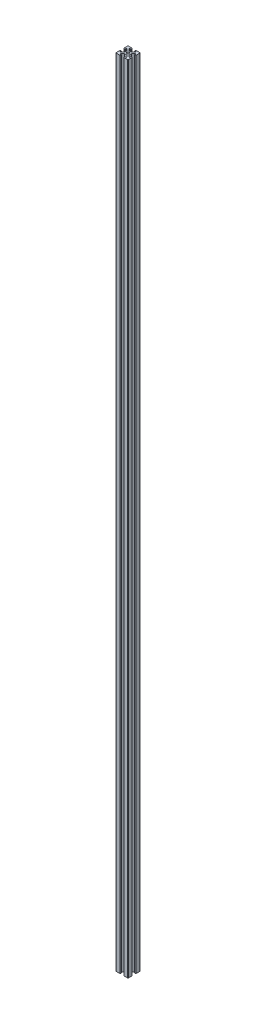
SolidWorks part; units mm, degrees
ref_plane "정면" through (0, 0, 0) normal (0, 0, 1) x (1, 0, 0)
ref_plane "윗면" through (0, 0, 0) normal (0, 1, 0) x (1, 0, 0)
ref_plane "우측면" through (0, 0, 0) normal (1, 0, 0) x (0, 0, -1)
sketch "스케치1" plane through (0, 0, 0) normal (0, 1, 0) x (1, 0, 0)
  line L0 (0, 4) -> (0, -4) construction
  line L1 (2, -4) -> (-2, -4)
  line L2 (-2, -4) -> (-5, -7)
  line L3 (-5, -7) -> (-5, -8) construction
  line L4 (-5, -8) -> (-2.6, -8) construction
  line L5 (-2.6, -8) -> (-2.6, -9.5) construction
  line L6 (-2.6, -9.5) -> (-3.1, -9.5)
  line L7 (-3.1, -9.5) -> (-3.1, -10)
  line L8 (-3.1, -10) -> (-9, -10)
  line L9 (-9, -10) -> (-9, -9) construction
  line L10 (-9, -10) -> (-10, -10) construction
  line L11 (-9, -9) -> (-10, -9) construction
  line L12 (-10, -10) -> (-10, -9) construction
  line L13 (3.1, -8) -> (3.1, -8.5) construction
  line L14 (2.6, -8.5) -> (3.1, -8.5) construction
  line L15 (2.6, -8) -> (2.6, -8.5) construction
  line L16 (-5, -7) -> (-5, -7.5)
  line L17 (-5, -8) -> (-4.5, -8) construction
  line L18 (-5, -8) -> (-5, -7.5) construction
  line L19 (-5, -7.5) -> (-4.5, -7.5) construction
  line L20 (-4.5, -8) -> (-4.5, -7.5) construction
  line L21 (-2.6, -9.5) -> (-2.6, -8.5)
  line L22 (-2.6, -8) -> (-3.1, -8) construction
  line L23 (-2.6, -8) -> (-2.6, -8.5) construction
  line L24 (-2.6, -8.5) -> (-3.1, -8.5) construction
  line L25 (-3.1, -8) -> (-3.1, -8.5) construction
  line L26 (-4.5, -8) -> (-3.1, -8)
  line L27 (2.6, -8) -> (3.1, -8) construction
  line L28 (4.5, -8) -> (4.5, -7.5) construction
  line L29 (5, -7.5) -> (4.5, -7.5) construction
  line L30 (5, -8) -> (5, -7.5) construction
  line L31 (5, -8) -> (4.5, -8) construction
  line L32 (10, -10) -> (10, -9) construction
  line L33 (9, -9) -> (10, -9) construction
  line L34 (9, -10) -> (10, -10) construction
  line L35 (9, -10) -> (9, -9) construction
  line L36 (2.6, -8) -> (2.6, -9.5) construction
  line L37 (5, -8) -> (2.6, -8) construction
  line L38 (5, -7) -> (5, -8) construction
  line L39 (4.5, -8) -> (3.1, -8)
  line L40 (2.6, -9.5) -> (2.6, -8.5)
  line L41 (5, -7) -> (5, -7.5)
  line L42 (3.1, -10) -> (9, -10)
  line L43 (3.1, -9.5) -> (3.1, -10)
  line L44 (2.6, -9.5) -> (3.1, -9.5)
  line L45 (2, -4) -> (5, -7)
  line L46 (-4, -2) -> (-4, 2)
  line L47 (-4, 2) -> (-7, 5)
  line L48 (-9.5, 2.6) -> (-9.5, 3.1)
  line L49 (-9.5, 3.1) -> (-10, 3.1)
  line L50 (-10, 3.1) -> (-10, 9)
  line L51 (-7, 5) -> (-7.5, 5)
  line L52 (-9.5, 2.6) -> (-8.5, 2.6)
  line L53 (-8, 4.5) -> (-8, 3.1)
  line L54 (-8, -4.5) -> (-8, -3.1)
  line L55 (-9.5, -2.6) -> (-8.5, -2.6)
  line L56 (-7, -5) -> (-7.5, -5)
  line L57 (-10, -3.1) -> (-10, -9)
  line L58 (-9.5, -3.1) -> (-10, -3.1)
  line L59 (-9.5, -2.6) -> (-9.5, -3.1)
  line L60 (-4, -2) -> (-7, -5)
  line L61 (4, 0) -> (-4, 0) construction
  line L62 (-7, 5) -> (-8, 5) construction
  line L63 (-8, 5) -> (-8, 2.6) construction
  line L64 (-8, 2.6) -> (-9.5, 2.6) construction
  line L65 (-10, 9) -> (-9, 9) construction
  line L66 (-10, 9) -> (-10, 10) construction
  line L67 (-9, 9) -> (-9, 10) construction
  line L68 (-10, 10) -> (-9, 10) construction
  line L69 (-8, -3.1) -> (-8.5, -3.1) construction
  line L70 (-8.5, -2.6) -> (-8.5, -3.1) construction
  line L71 (-8, -2.6) -> (-8.5, -2.6) construction
  line L72 (-8, 5) -> (-8, 4.5) construction
  line L73 (-8, 5) -> (-7.5, 5) construction
  line L74 (-7.5, 5) -> (-7.5, 4.5) construction
  line L75 (-8, 4.5) -> (-7.5, 4.5) construction
  line L76 (-8, 2.6) -> (-8, 3.1) construction
  line L77 (-8, 2.6) -> (-8.5, 2.6) construction
  line L78 (-8.5, 2.6) -> (-8.5, 3.1) construction
  line L79 (-8, 3.1) -> (-8.5, 3.1) construction
  line L80 (-8, -2.6) -> (-8, -3.1) construction
  line L81 (-8, -4.5) -> (-7.5, -4.5) construction
  line L82 (-7.5, -5) -> (-7.5, -4.5) construction
  line L83 (-8, -5) -> (-7.5, -5) construction
  line L84 (-8, -5) -> (-8, -4.5) construction
  line L85 (-10, -10) -> (-9, -10) construction
  line L86 (-9, -9) -> (-9, -10) construction
  line L87 (-10, -9) -> (-10, -10) construction
  line L88 (-10, -9) -> (-9, -9) construction
  line L89 (-8, -2.6) -> (-9.5, -2.6) construction
  line L90 (-8, -5) -> (-8, -2.6) construction
  line L91 (-7, -5) -> (-8, -5) construction
  line L92 (-2, 4) -> (2, 4)
  line L93 (2, 4) -> (5, 7)
  line L94 (2.6, 9.5) -> (3.1, 9.5)
  line L95 (3.1, 9.5) -> (3.1, 10)
  line L96 (3.1, 10) -> (9, 10)
  line L97 (5, 7) -> (5, 7.5)
  line L98 (2.6, 9.5) -> (2.6, 8.5)
  line L99 (4.5, 8) -> (3.1, 8)
  line L100 (-4.5, 8) -> (-3.1, 8)
  line L101 (-2.6, 9.5) -> (-2.6, 8.5)
  line L102 (-5, 7) -> (-5, 7.5)
  line L103 (-3.1, 10) -> (-9, 10)
  line L104 (-3.1, 9.5) -> (-3.1, 10)
  line L105 (-2.6, 9.5) -> (-3.1, 9.5)
  line L106 (-2, 4) -> (-5, 7)
  line L107 (0, -4) -> (0, 4) construction
  line L108 (5, 7) -> (5, 8) construction
  line L109 (5, 8) -> (2.6, 8) construction
  line L110 (2.6, 8) -> (2.6, 9.5) construction
  line L111 (9, 10) -> (9, 9) construction
  line L112 (9, 10) -> (10, 10) construction
  line L113 (9, 9) -> (10, 9) construction
  line L114 (10, 10) -> (10, 9) construction
  line L115 (-3.1, 8) -> (-3.1, 8.5) construction
  line L116 (-2.6, 8.5) -> (-3.1, 8.5) construction
  line L117 (-2.6, 8) -> (-2.6, 8.5) construction
  line L118 (5, 8) -> (4.5, 8) construction
  line L119 (5, 8) -> (5, 7.5) construction
  line L120 (5, 7.5) -> (4.5, 7.5) construction
  line L121 (4.5, 8) -> (4.5, 7.5) construction
  line L122 (2.6, 8) -> (3.1, 8) construction
  line L123 (2.6, 8) -> (2.6, 8.5) construction
  line L124 (2.6, 8.5) -> (3.1, 8.5) construction
  line L125 (3.1, 8) -> (3.1, 8.5) construction
  line L126 (-2.6, 8) -> (-3.1, 8) construction
  line L127 (-4.5, 8) -> (-4.5, 7.5) construction
  line L128 (-5, 7.5) -> (-4.5, 7.5) construction
  line L129 (-5, 8) -> (-5, 7.5) construction
  line L130 (-5, 8) -> (-4.5, 8) construction
  line L131 (-10, 10) -> (-10, 9) construction
  line L132 (-9, 9) -> (-10, 9) construction
  line L133 (-9, 10) -> (-10, 10) construction
  line L134 (-9, 10) -> (-9, 9) construction
  line L135 (-2.6, 8) -> (-2.6, 9.5) construction
  line L136 (-5, 8) -> (-2.6, 8) construction
  line L137 (-5, 7) -> (-5, 8) construction
  line L138 (4, 2) -> (4, -2)
  line L139 (4, -2) -> (7, -5)
  line L140 (9.5, -2.6) -> (9.5, -3.1)
  line L141 (9.5, -3.1) -> (10, -3.1)
  line L142 (10, -3.1) -> (10, -9)
  line L143 (7, -5) -> (7.5, -5)
  line L144 (9.5, -2.6) -> (8.5, -2.6)
  line L145 (8, -4.5) -> (8, -3.1)
  line L146 (8, 4.5) -> (8, 3.1)
  line L147 (9.5, 2.6) -> (8.5, 2.6)
  line L148 (7, 5) -> (7.5, 5)
  line L149 (10, 3.1) -> (10, 9)
  line L150 (9.5, 3.1) -> (10, 3.1)
  line L151 (9.5, 2.6) -> (9.5, 3.1)
  line L152 (4, 2) -> (7, 5)
  line L153 (-4, 0) -> (4, 0) construction
  line L154 (7, -5) -> (8, -5) construction
  line L155 (8, -5) -> (8, -2.6) construction
  line L156 (8, -2.6) -> (9.5, -2.6) construction
  line L157 (10, -9) -> (9, -9) construction
  line L158 (10, -9) -> (10, -10) construction
  line L159 (9, -9) -> (9, -10) construction
  line L160 (10, -10) -> (9, -10) construction
  line L161 (8, 3.1) -> (8.5, 3.1) construction
  line L162 (8.5, 2.6) -> (8.5, 3.1) construction
  line L163 (8, 2.6) -> (8.5, 2.6) construction
  line L164 (8, -5) -> (8, -4.5) construction
  line L165 (8, -5) -> (7.5, -5) construction
  line L166 (7.5, -5) -> (7.5, -4.5) construction
  line L167 (8, -4.5) -> (7.5, -4.5) construction
  line L168 (8, -2.6) -> (8, -3.1) construction
  line L169 (8, -2.6) -> (8.5, -2.6) construction
  line L170 (8.5, -2.6) -> (8.5, -3.1) construction
  line L171 (8, -3.1) -> (8.5, -3.1) construction
  line L172 (8, 2.6) -> (8, 3.1) construction
  line L173 (8, 4.5) -> (7.5, 4.5) construction
  line L174 (7.5, 5) -> (7.5, 4.5) construction
  line L175 (8, 5) -> (7.5, 5) construction
  line L176 (8, 5) -> (8, 4.5) construction
  line L177 (10, 10) -> (9, 10) construction
  line L178 (9, 9) -> (9, 10) construction
  line L179 (10, 9) -> (10, 10) construction
  line L180 (10, 9) -> (9, 9) construction
  line L181 (8, 2.6) -> (9.5, 2.6) construction
  line L182 (8, 5) -> (8, 2.6) construction
  line L183 (7, 5) -> (8, 5) construction
  circle A0 centre (0, 0) radius 2.1
  arc A1 (-5, -7.5) -> (-4.5, -8) centre (-4.5, -7.5) ccw
  arc A2 (-3.1, -8) -> (-2.6, -8.5) centre (-3.1, -8.5) cw
  arc A3 (-9, -10) -> (-9.7071, -9.7071) centre (-9, -9) cw
  arc A4 (9, -10) -> (9.7071, -9.7071) centre (9, -9) ccw
  arc A5 (3.1, -8) -> (2.6, -8.5) centre (3.1, -8.5) ccw
  arc A6 (5, -7.5) -> (4.5, -8) centre (4.5, -7.5) cw
  arc A7 (-7.5, 5) -> (-8, 4.5) centre (-7.5, 4.5) ccw
  arc A8 (-8, 3.1) -> (-8.5, 2.6) centre (-8.5, 3.1) cw
  arc A9 (-10, 9) -> (-9.7071, 9.7071) centre (-9, 9) cw
  arc A10 (-10, -9) -> (-9.7071, -9.7071) centre (-9, -9) ccw
  arc A11 (-8, -3.1) -> (-8.5, -2.6) centre (-8.5, -3.1) ccw
  arc A12 (-7.5, -5) -> (-8, -4.5) centre (-7.5, -4.5) cw
  arc A13 (5, 7.5) -> (4.5, 8) centre (4.5, 7.5) ccw
  arc A14 (3.1, 8) -> (2.6, 8.5) centre (3.1, 8.5) cw
  arc A15 (9, 10) -> (9.7071, 9.7071) centre (9, 9) cw
  arc A16 (-9, 10) -> (-9.7071, 9.7071) centre (-9, 9) ccw
  arc A17 (-3.1, 8) -> (-2.6, 8.5) centre (-3.1, 8.5) ccw
  arc A18 (-5, 7.5) -> (-4.5, 8) centre (-4.5, 7.5) cw
  arc A19 (7.5, -5) -> (8, -4.5) centre (7.5, -4.5) ccw
  arc A20 (8, -3.1) -> (8.5, -2.6) centre (8.5, -3.1) cw
  arc A21 (10, -9) -> (9.7071, -9.7071) centre (9, -9) cw
  arc A22 (10, 9) -> (9.7071, 9.7071) centre (9, 9) ccw
  arc A23 (8, 3.1) -> (8.5, 2.6) centre (8.5, 3.1) ccw
  arc A24 (7.5, 5) -> (8, 4.5) centre (7.5, 4.5) cw
  point P6 (0, 0)
  point P9 (0, -4)
  point P52 (-4, 0)
  point P92 (0, 4)
  point P132 (4, 0)
  point P167 (0, 0)
  dimension "D1" = 4.2
  dimension "D9" = 1
  dimension "D2" = 4
  dimension "D3" = 4
  dimension "D4" = 3
  dimension "D5" = 1
  dimension "D6" = 2
  dimension "D7" = 2.6
  dimension "D8" = 3.1
  dimension "D10" = 1
  dimension "D11" = 0.5
  dimension "D12" = 0.5
  dimension "D13" = 0.5
  dimension "D14" = 5
  dimension "D15" = 45
  dimension "D16" = 1
  dimension "D17" = 10
  dimension "D18" = 4
extrude "보스-돌출1" add sketch "스케치1" along normal blind 1300
